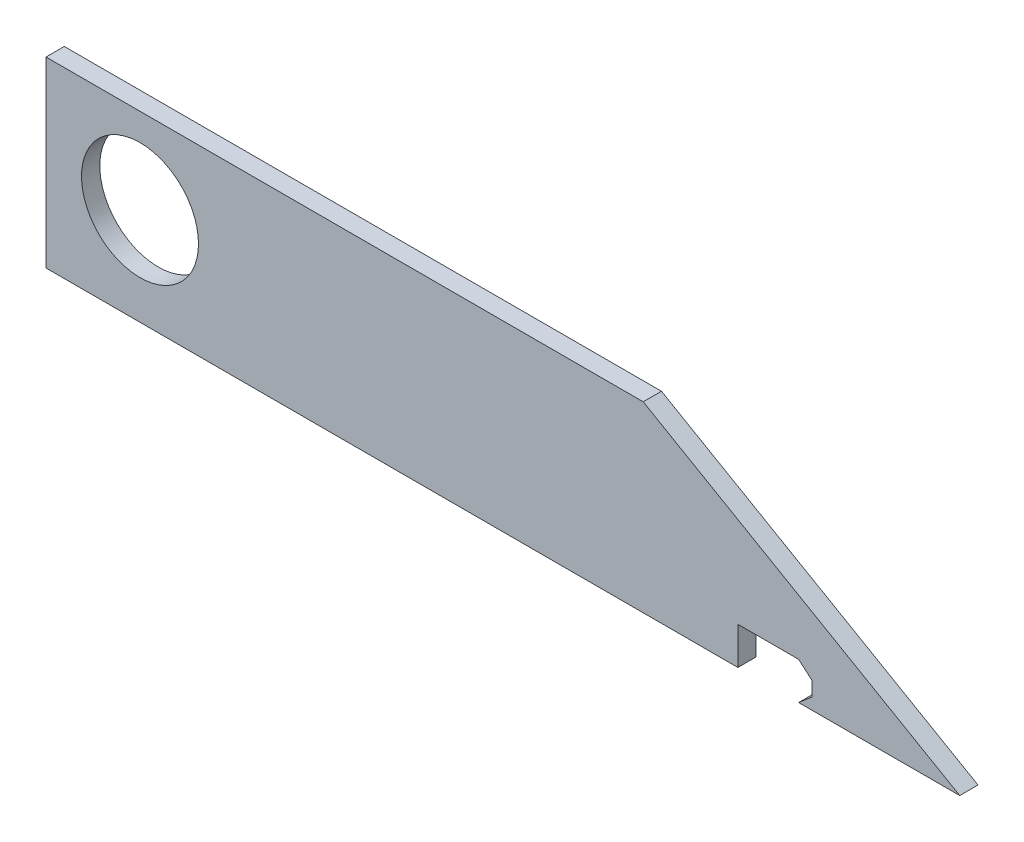
SolidWorks part; units mm, degrees
ref_plane "Front Plane" through (0, 0, 0) normal (0, 0, 1) x (1, 0, 0)
ref_plane "Top Plane" through (0, 0, 0) normal (0, 1, 0) x (1, 0, 0)
ref_plane "Right Plane" through (0, 0, 0) normal (1, 0, 0) x (0, 0, -1)
sketch "Sketch2" plane through (0, 0, 0) normal (0, 0, 1) x (1, 0, 0)
  line L0 (-63.5, 2.4) -> (63.5, 2.4)
  line L1 (63.5, 2.4) -> (19.5059, 27.8)
  line L2 (19.5059, 27.8) -> (-63.5, 27.8)
  line L3 (-63.5, 27.8) -> (-63.5, 2.4)
  line L4 (65.5, 5.8641) -> (63.5, 2.4) construction
  dimension "D1" = 25.4
  dimension "D2" = 30
extrude "Boss-Extrude1" add sketch "Sketch2" against normal blind 2.54
sketch "Sketch3" plane through (0, 0, 0) normal (0, 0, 1) x (1, 0, 0)
  circle A0 centre (-50.4348, 15.9061) radius 8.128
extrude "Cut-Extrude1" cut sketch "Sketch3" against normal blind 2.54
sketch "Sketch4" plane through (0, 0, -2.54) normal (0, 0, -1) x (-1, 0, 0)
  line L0 (-41.1054, 7.6) -> (-32.6673, 7.6)
  line L1 (-32.6673, 7.6) -> (-32.6673, 2.4)
  line L2 (63.5, 2.4) -> (-63.5, 2.4) construction
  line L3 (-32.6673, 7.6) -> (-32.6673, 2.4) construction
  line L4 (-32.6673, 2.4) -> (-41.1054, 2.4)
  line L5 (-41.1054, 2.4) -> (-42.9673, 4) construction
  line L6 (-41.1054, 2.4) -> (-42.9673, 4)
  line L7 (-42.9673, 4) -> (-42.9673, 6)
  line L8 (-42.9673, 6) -> (-41.1054, 7.6) construction
  line L9 (-42.9673, 4) -> (-42.9673, 6) construction
  line L10 (-42.9673, 6) -> (-41.1054, 7.6)
extrude "Cut-Extrude2" cut sketch "Sketch4" against normal through all
